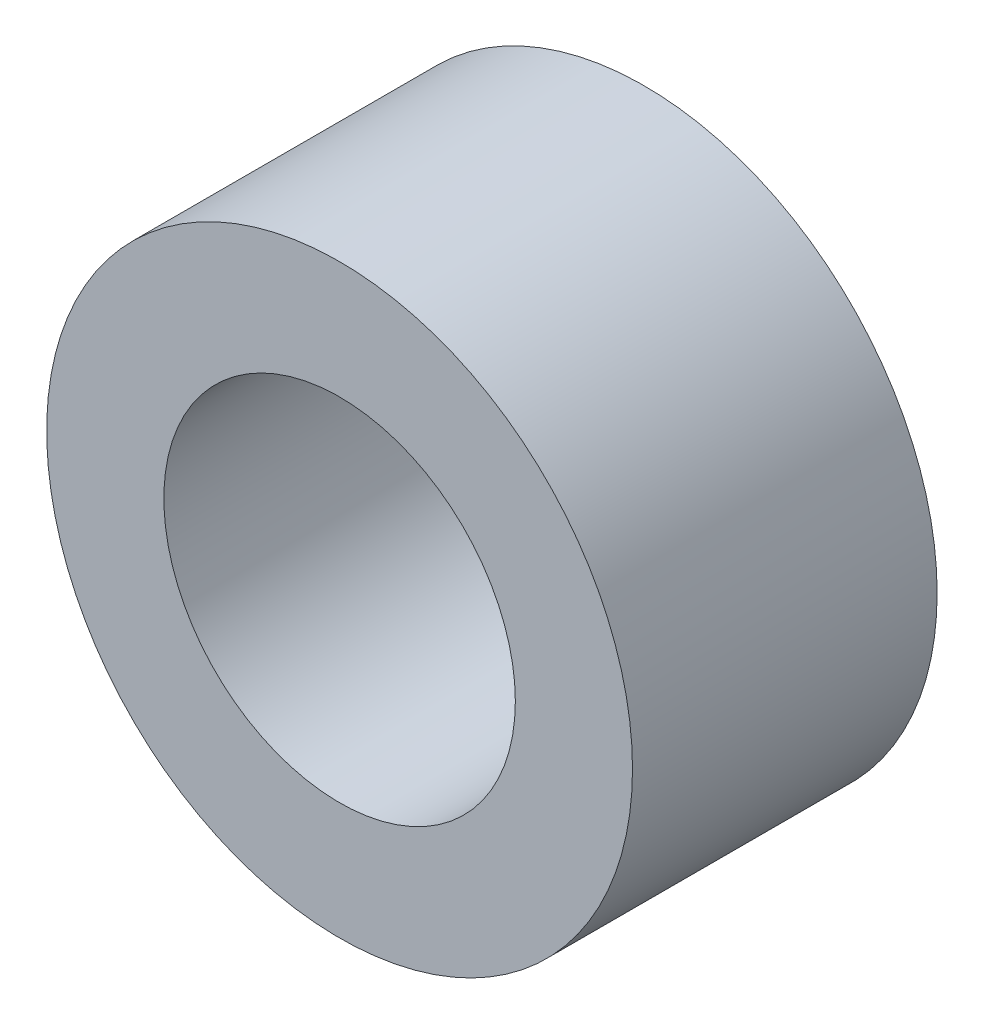
SolidWorks part; units mm, degrees
material "ﾎﾟﾘｵｷｼﾒﾁﾚﾝ(POM)ｱｾﾀｰﾙ共重合体"
ref_plane "Front Plane" through (0, 0, 0) normal (0, 0, 1) x (1, 0, 0)
ref_plane "Top Plane" through (0, 0, 0) normal (0, 1, 0) x (1, 0, 0)
ref_plane "Right Plane" through (0, 0, 0) normal (1, 0, 0) x (0, 0, -1)
sketch "Sketch2" plane through (0, 0, 0) normal (0, 0, 1) x (1, 0, 0)
  circle A0 centre (0, 0) radius 2.5
  circle A1 centre (0, 0) radius 1.5
  dimension "D1" = 3
  dimension "D2" = 5
  dimension "D3" = 5
extrude "Boss-Extrude1" add sketch "Sketch2" along normal blind 2.6
